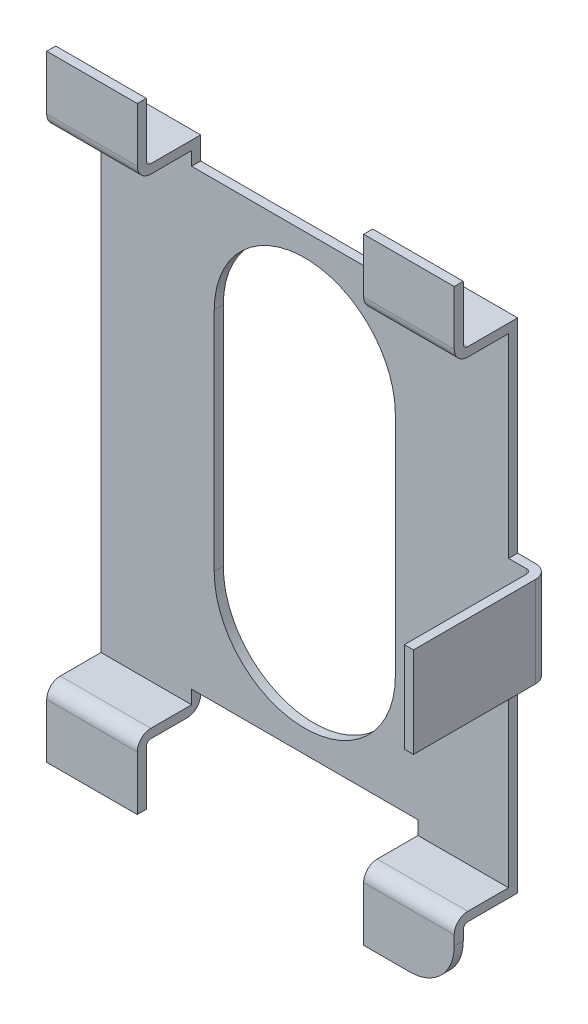
SolidWorks part; units mm, degrees
material "AISI 316 Stainless Steel Sheet (SS)"
ref_plane "Front Plane" through (0, 0, 0) normal (0, 0, 1) x (1, 0, 0)
ref_plane "Top Plane" through (0, 0, 0) normal (0, 1, 0) x (1, 0, 0)
ref_plane "Right Plane" through (0, 0, 0) normal (1, 0, 0) x (0, 0, -1)
ref_plane "Plane1" through (0, 0, 0) normal (1, 0, 0) x (0, -1, 0)
sketch "Sketch1" plane through (0, 0, 0) normal (1, 0, 0) x (0, -1, 0)
  line L0 (2.65, 0) -> (2.65, -0.45)
  line L1 (-2.65, 0) -> (-2.65, -0.45)
  line L2 (-2.65, 0) -> (2.65, 0)
  line L3 (2.8, -0.6) -> (3.4, -0.6)
  line L4 (-2.8, -0.6) -> (-3.4, -0.6)
  arc A0 (2.65, -0.45) -> (2.8, -0.6) centre (2.8, -0.45) ccw
  arc A1 (-2.8, -0.6) -> (-2.65, -0.45) centre (-2.8, -0.45) ccw
extrude "Extrude-Thin2" add sketch "Sketch1" along normal blind 2.25 and the other way blind 2.25 thin thin type one direction wall 0.1
ref_plane "Plane2" through (0, 0, 0) normal (0, 1, 0) x (-1, 0, 0)
sketch "Sketch2" plane through (0, 0, 0) normal (0, 1, 0) x (-1, 0, 0)
  line L0 (-1.25, 0.8) -> (1.25, 0.8)
  line L1 (1.25, 0.8) -> (1.25, 0)
  line L2 (1.25, 0) -> (-1.25, 0)
  line L3 (-1.25, 0) -> (-1.25, 0.8)
extrude "Extrude1" cut sketch "Sketch2" along normal blind 4 and the other way blind 4
ref_plane "Plane3" through (0, 0, 0) normal (0, 0, 1) x (0, -1, 0)
sketch "S2D0010" plane through (0, 0, 0) normal (0, 0, 1) x (0, -1, 0)
  line L0 (1.25, 1) -> (-1.25, 1)
  line L1 (-1.25, -1) -> (1.25, -1)
  line L2 (2.5, 1.25) -> (3, 1.25)
  line L3 (3, 1.25) -> (3, -1.25)
  line L4 (3, -1.25) -> (2.5, -1.25)
  line L5 (2.5, -1.25) -> (2.5, 1.25)
  line L6 (-3, 1.25) -> (-2.5, 1.25)
  line L7 (-2.5, 1.25) -> (-2.5, -1.25)
  line L8 (-2.5, -1.25) -> (-3, -1.25)
  line L9 (-3, -1.25) -> (-3, 1.25)
  arc A0 (1.25, -1) -> (1.25, 1) centre (1.25, 0) ccw
  arc A1 (-1.25, 1) -> (-1.25, -1) centre (-1.25, 0) ccw
extrude "Extrude2" cut sketch "S2D0010" against normal blind 0.17
ref_plane "Plane4" through (0, 0, 0) normal (0, 1, 0) x (1, 0, 0)
sketch "S2D0012" plane through (0, 0, 0) normal (0, 1, 0) x (1, 0, 0)
  line L0 (2.25, 0) -> (2.45, 0)
  line L1 (2.5, -0.05) -> (2.5, -1.4)
  arc A0 (2.5, -0.05) -> (2.45, 0) centre (2.45, -0.05) ccw
extrude "Extrude-Thin3" add sketch "S2D0012" along normal blind 0.5 and the other way blind 0.5 thin thin type one direction reverse wall 0.1
fillet "Fillet1" radius 0.15 1 edges at (-1.75, -2.75, -0.1)
fillet "Fillet2" radius 0.49 1 edges at (2.25, -3.4, 0.55)
